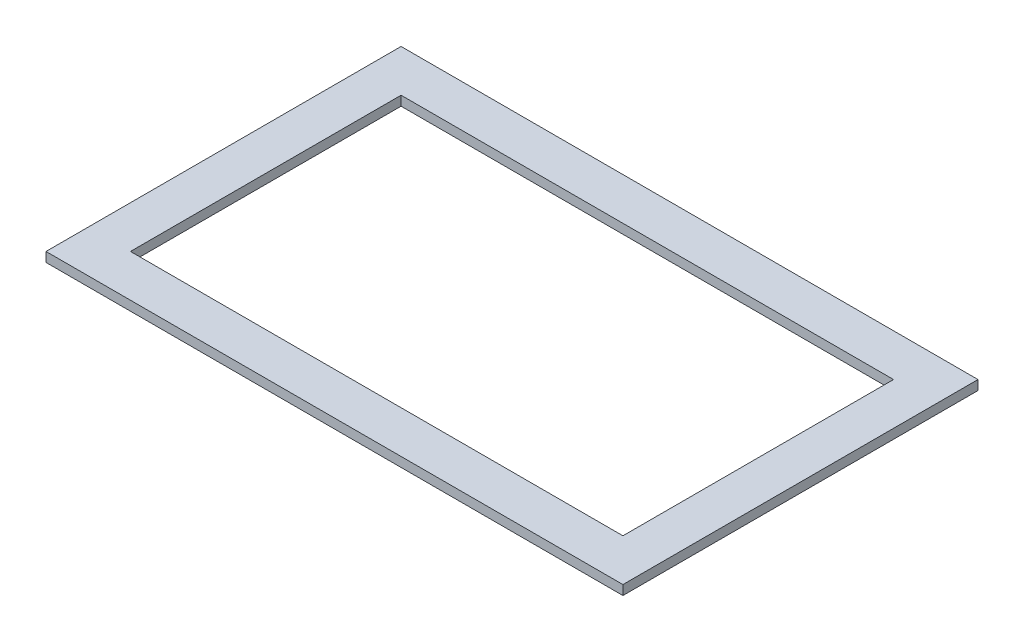
SolidWorks part; units mm, degrees
ref_plane "Front Plane" through (0, 0, 0) normal (0, 0, 1) x (1, 0, 0)
ref_plane "Top Plane" through (0, 0, 0) normal (0, 1, 0) x (1, 0, 0)
ref_plane "Right Plane" through (0, 0, 0) normal (1, 0, 0) x (0, 0, -1)
sketch "Sketch1" plane through (0, 0, 0) normal (0, 1, 0) x (1, 0, 0)
  line L1 (-51.6515, -28.3834) -> (51.6515, -28.3834)
  line L2 (-51.6515, -28.3834) -> (-51.6515, 28.3834)
  line L3 (-51.6515, 28.3834) -> (51.6515, 28.3834)
  line L4 (51.6515, -28.3834) -> (51.6515, 28.3834)
  line L5 (-51.6515, -28.3834) -> (51.6515, 28.3834) construction
  line L6 (-51.6515, 28.3834) -> (51.6515, -28.3834) construction
  line L7 (-60.5097, -37.2415) -> (60.5097, -37.2415)
  line L8 (-60.5097, -37.2415) -> (-60.5097, 37.2415)
  line L9 (-60.5097, 37.2415) -> (60.5097, 37.2415)
  line L10 (60.5097, -37.2415) -> (60.5097, 37.2415)
  line L11 (-60.5097, -37.2415) -> (60.5097, 37.2415) construction
  line L12 (-60.5097, 37.2415) -> (60.5097, -37.2415) construction
  point P0 (0, 0)
  point P6 (0, 0)
extrude "Boss-Extrude1" add sketch "Sketch1" along normal blind 2
